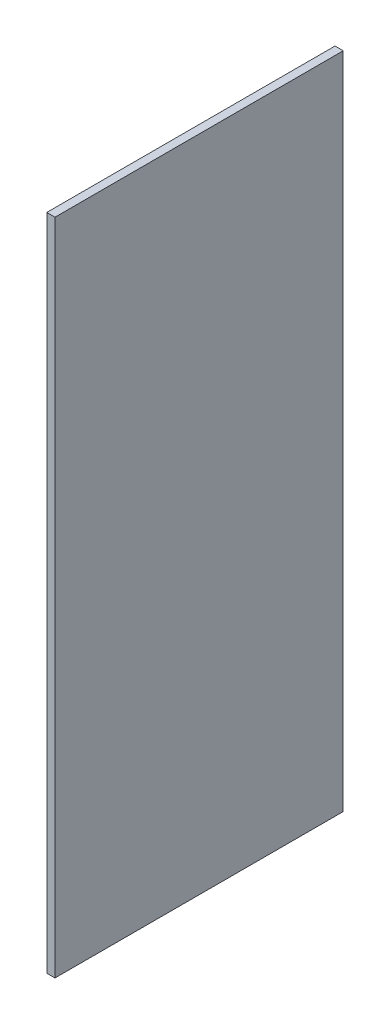
SolidWorks part; units mm, degrees
ref_plane "Front Plane" through (0, 0, 0) normal (0, 0, 1) x (1, 0, 0)
ref_plane "Top Plane" through (0, 0, 0) normal (0, 1, 0) x (1, 0, 0)
ref_plane "Right Plane" through (0, 0, 0) normal (1, 0, 0) x (0, 0, -1)
sketch "Sketch1" plane through (0, 0, 0) normal (1, 0, 0) x (0, 0, -1)
  line L1 (-44.45, -101.6) -> (44.45, -101.6)
  line L2 (-44.45, -101.6) -> (-44.45, 101.6)
  line L3 (-44.45, 101.6) -> (44.45, 101.6)
  line L4 (44.45, -101.6) -> (44.45, 101.6)
  line L5 (-44.45, -101.6) -> (44.45, 101.6) construction
  line L6 (-44.45, 101.6) -> (44.45, -101.6) construction
  point P0 (0, 0)
  dimension "D1" = 88.9
  dimension "D2" = 203.2
extrude "Boss-Extrude1" add sketch "Sketch1" along normal blind 2.54
